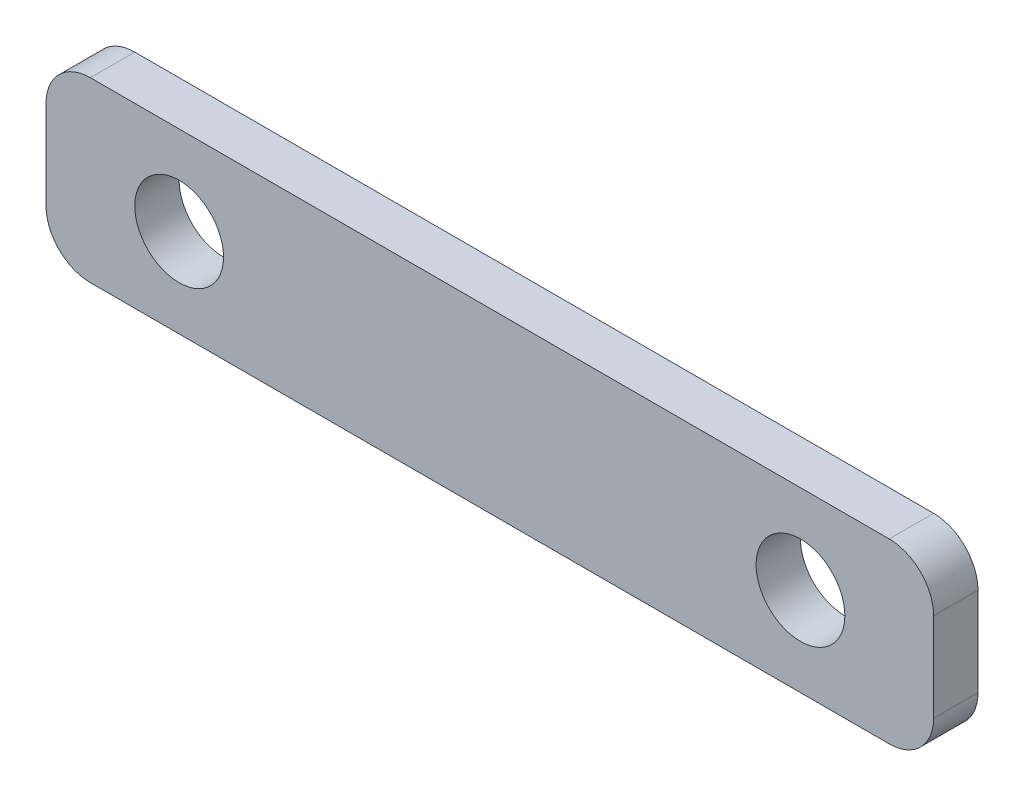
SolidWorks part; units mm, degrees
ref_plane "Front Plane" through (0, 0, 0) normal (0, 0, 1) x (1, 0, 0)
ref_plane "Top Plane" through (0, 0, 0) normal (0, 1, 0) x (1, 0, 0)
ref_plane "Right Plane" through (0, 0, 0) normal (1, 0, 0) x (0, 0, -1)
sketch "Sketch1" plane through (0, 0, 0) normal (0, 0, 1) x (1, 0, 0)
  line L0 (-200, 150.6839) -> (-170, 150.6839) construction
  line L2 (-190, 150.6839) -> (-10, 150.6839)
  line L3 (-200, 140.6839) -> (-200, 120.6839)
  line L4 (-190, 110.6839) -> (-10, 110.6839)
  line L5 (0, 140.6839) -> (0, 120.6839)
  line L6 (-200, 150.6839) -> (0, 110.6839) construction
  line L7 (-200, 110.6839) -> (0, 150.6839) construction
  line L8 (0, 150.6839) -> (-30, 150.6839) construction
  line L9 (-170, 150.6839) -> (-170, 110.6839) construction
  line L10 (-30, 150.6839) -> (-30, 110.6839) construction
  arc A0 (-10, 110.6839) -> (0, 120.6839) centre (-10, 120.6839) ccw
  arc A1 (-10, 150.6839) -> (0, 140.6839) centre (-10, 140.6839) cw
  arc A2 (-200, 120.6839) -> (-190, 110.6839) centre (-190, 120.6839) ccw
  arc A3 (-190, 150.6839) -> (-200, 140.6839) centre (-190, 140.6839) ccw
  circle A4 centre (-170, 130.6839) radius 10
  circle A5 centre (-30, 130.6839) radius 10
  point P0 (-100, 130.6839)
  dimension "D3" = 10
  dimension "D1" = 200
  dimension "D2" = 40
extrude "Boss-Extrude1" add sketch "Sketch1" along normal mid plane 10
